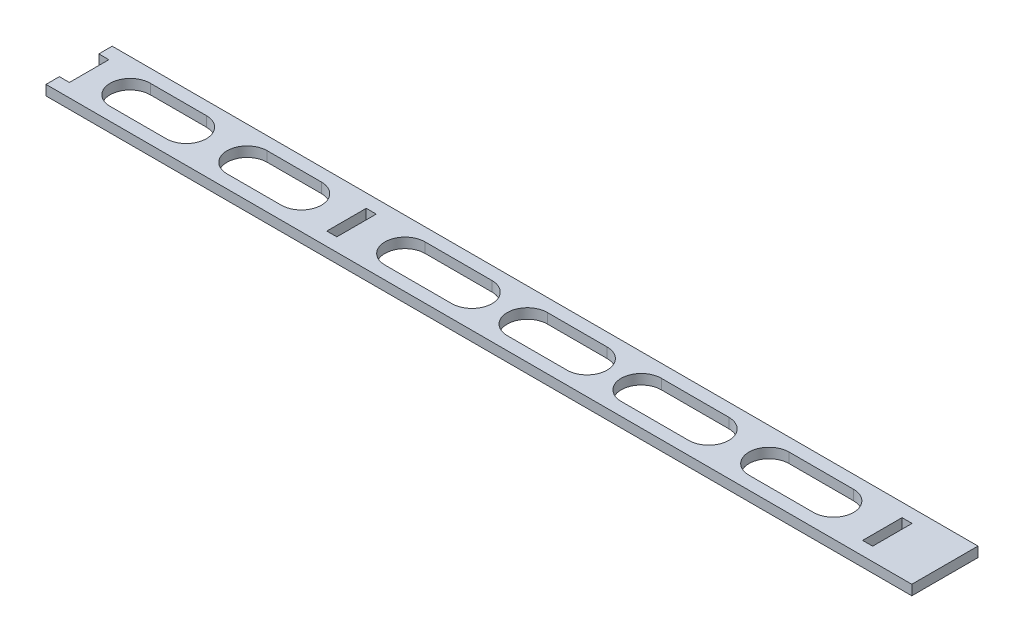
SolidWorks part; units mm, degrees
ref_plane "Front Plane" through (0, 0, 0) normal (0, 0, 1) x (1, 0, 0)
ref_plane "Top Plane" through (0, 0, 0) normal (0, 1, 0) x (1, 0, 0)
ref_plane "Right Plane" through (0, 0, 0) normal (1, 0, 0) x (0, 0, -1)
sketch "Sketch1" plane through (0, 0, 0) normal (0, 1, 0) x (1, 0, 0)
  line L1 (0, 0) -> (259, 0)
  line L2 (0, 0) -> (0, 19.8)
  line L3 (0, 19.8) -> (259, 19.8)
  line L4 (259, 0) -> (259, 19.8)
  dimension "D1" = 259
  dimension "D2" = 19.8
extrude "Boss-Extrude1" add sketch "Sketch1" along normal blind 3
sketch "Sketch2" plane through (0, 3, 0) normal (0, 1, 0) x (1, 0, 0)
  line L0 (0, 19.8) -> (0, 0) construction
  line L1 (0, 15.8) -> (3, 15.8)
  line L2 (0, 15.8) -> (0, 4)
  line L3 (0, 4) -> (3, 4)
  line L4 (3, 15.8) -> (3, 4)
  line L5 (0, 0) -> (259, 0) construction
  line L6 (80, 15.8) -> (83, 15.8)
  line L7 (80, 15.8) -> (80, 4)
  line L8 (80, 4) -> (83, 4)
  line L9 (83, 15.8) -> (83, 4)
  line L10 (240.28, 15.8) -> (243.28, 15.8)
  line L11 (240.28, 15.8) -> (240.28, 4)
  line L12 (240.28, 4) -> (243.28, 4)
  line L13 (243.28, 15.8) -> (243.28, 4)
  line L14 (259, 19.8) -> (0, 19.8) construction
  dimension "D1" = 160.28
  dimension "D2" = 80
  dimension "D3" = 3
  dimension "D4" = 4
  dimension "D5" = 4
extrude "Cut-Extrude1" cut sketch "Sketch2" against normal blind 3
sketch "Sketch3" plane through (0, 3, 0) normal (0, 1, 0) x (1, 0, 0)
  line L0 (15.2915, 9.9) -> (32.0577, 9.9) construction
  line L1 (15.2915, 15.9) -> (32.0577, 15.9)
  line L2 (15.2915, 3.9) -> (32.0577, 3.9)
  line L3 (97.5, 9.9) -> (117.5113, 9.9) construction
  line L4 (97.5, 15.9) -> (117.5113, 15.9)
  line L5 (97.5, 3.9) -> (117.5113, 3.9)
  line L6 (134.0972, 9.9) -> (151.9451, 9.9) construction
  line L7 (134.0972, 15.9) -> (151.9451, 15.9)
  line L8 (134.0972, 3.9) -> (151.9451, 3.9)
  line L9 (50.2661, 9.9) -> (66.4915, 9.9) construction
  line L10 (50.2661, 15.9) -> (66.4915, 15.9)
  line L11 (80, 15.8) -> (80, 4) construction
  line L12 (50.2661, 3.9) -> (66.4915, 3.9)
  line L13 (168.1704, 9.9) -> (188.362, 9.9) construction
  line L14 (168.1704, 15.9) -> (188.362, 15.9)
  line L15 (168.1704, 3.9) -> (188.362, 3.9)
  line L16 (206.3902, 9.9) -> (225.6803, 9.9) construction
  line L17 (206.3902, 15.9) -> (225.6803, 15.9)
  line L18 (206.3902, 3.9) -> (225.6803, 3.9)
  arc A0 (15.2915, 15.9) -> (15.2915, 3.9) centre (15.2915, 9.9) ccw
  arc A1 (32.0577, 3.9) -> (32.0577, 15.9) centre (32.0577, 9.9) ccw
  arc A2 (97.5, 15.9) -> (97.5, 3.9) centre (97.5, 9.9) ccw
  arc A3 (117.5113, 3.9) -> (117.5113, 15.9) centre (117.5113, 9.9) ccw
  arc A4 (134.0972, 15.9) -> (134.0972, 3.9) centre (134.0972, 9.9) ccw
  arc A5 (151.9451, 3.9) -> (151.9451, 15.9) centre (151.9451, 9.9) ccw
  arc A6 (50.2661, 15.9) -> (50.2661, 3.9) centre (50.2661, 9.9) ccw
  arc A7 (66.4915, 3.9) -> (66.4915, 15.9) centre (66.4915, 9.9) ccw
  arc A8 (168.1704, 15.9) -> (168.1704, 3.9) centre (168.1704, 9.9) ccw
  arc A9 (188.362, 3.9) -> (188.362, 15.9) centre (188.362, 9.9) ccw
  arc A10 (206.3902, 15.9) -> (206.3902, 3.9) centre (206.3902, 9.9) ccw
  arc A11 (225.6803, 3.9) -> (225.6803, 15.9) centre (225.6803, 9.9) ccw
  point P2 (23.6746, 9.9)
  point P7 (107.5056, 9.9)
  point P14 (143.0211, 9.9)
  point P21 (58.3788, 9.9)
  point P28 (80, 9.9)
  point P31 (178.2662, 9.9)
  point P38 (216.0353, 9.9)
  point P45 (134.0972, 9.9)
  point P46 (66.4915, 9.9)
  dimension "D1" = 6
extrude "Cut-Extrude2" cut sketch "Sketch3" against normal blind 3
